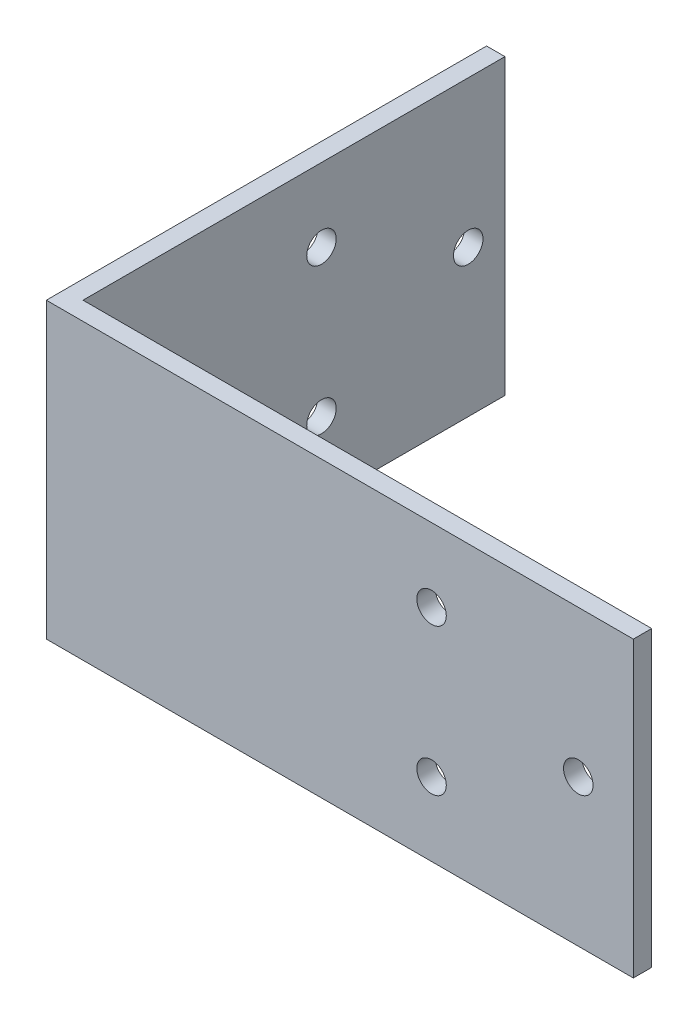
SolidWorks part; units mm, degrees
ref_plane "Front Plane" through (0, 0, 0) normal (0, 0, 1) x (1, 0, 0)
ref_plane "Top Plane" through (0, 0, 0) normal (0, 1, 0) x (1, 0, 0)
ref_plane "Right Plane" through (0, 0, 0) normal (1, 0, 0) x (0, 0, -1)
sketch "Sketch1" plane through (0, 0, 0) normal (0, 1, 0) x (1, 0, 0)
  line L2 (0, 0) -> (0, 76.2)
  line L3 (0, 76.2) -> (3.175, 76.2)
  line L4 (3.175, 3.175) -> (3.175, 76.2)
  line L5 (0, 0) -> (101.6, 0)
  line L7 (3.175, 3.175) -> (101.6, 3.175)
  line L8 (101.6, 0) -> (101.6, 3.175)
  dimension "D1" = 76.2
  dimension "D2" = 101.6
  dimension "D3" = 3.175
  dimension "D4" = 3.175
extrude "Boss-Extrude1" add sketch "Sketch1" along normal blind 50.8
sketch "Sketch2" plane through (0, 0, 0) normal (0, 0, 1) x (1, 0, 0)
  line L0 (101.6, 50.8) -> (101.6, 0) construction
  line L4 (92.075, 25.4) -> (66.675, 25.4) construction
  line L7 (66.675, 38.1) -> (66.675, 12.7) construction
  circle A0 centre (92.075, 25.4) radius 2.5527
  circle A1 centre (66.675, 38.1) radius 2.5527
  circle A2 centre (66.675, 12.7) radius 2.5527
  point P2 (66.675, 25.4)
  point P4 (101.6, 25.4)
  dimension "D2" = 5.1054
  dimension "D1" = 9.525
  dimension "D3" = 25.4
  dimension "D4" = 25.4
extrude "Cut-Extrude1" cut sketch "Sketch2" against normal blind 50.8
sketch "Sketch3" plane through (0, 0, 0) normal (-1, 0, 0) x (0, 0, 1)
  line L0 (-44.45, 38.1) -> (-44.45, 12.7) construction
  line L1 (-76.2, 50.8) -> (-76.2, 0) construction
  line L2 (-69.85, 25.4) -> (-44.45, 25.4) construction
  circle A0 centre (-69.85, 25.4) radius 2.5527
  circle A1 centre (-44.45, 38.1) radius 2.5527
  circle A2 centre (-44.45, 12.7) radius 2.5527
  point P9 (-76.2, 25.4)
  dimension "D3" = 5.1054
  dimension "D1" = 25.4
  dimension "D2" = 25.4
  dimension "D4" = 6.35
extrude "Cut-Extrude2" cut sketch "Sketch3" against normal blind 50.8
